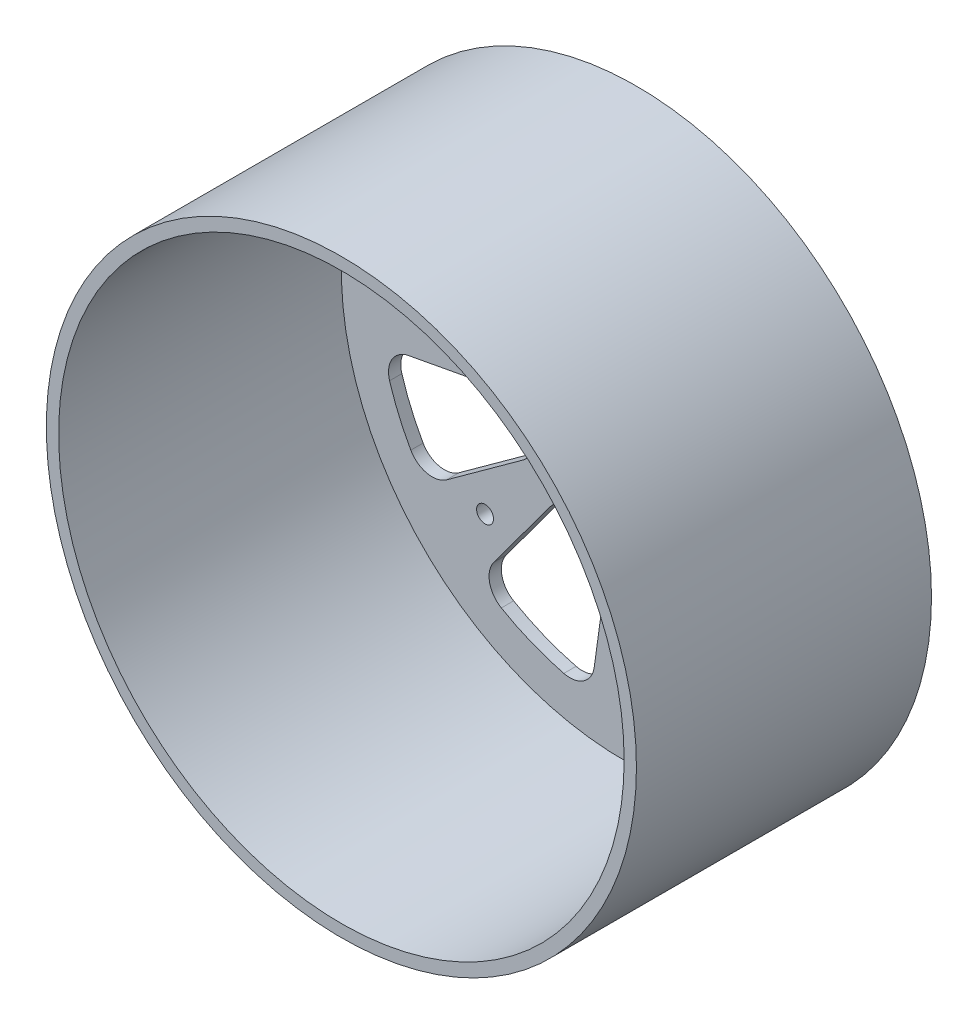
SolidWorks part; units mm, degrees
material "6061-T6 (SS)"
ref_plane "Front Plane" through (0, 0, 0) normal (0, 0, 1) x (1, 0, 0)
ref_plane "Top Plane" through (0, 0, 0) normal (0, 1, 0) x (1, 0, 0)
ref_plane "Right Plane" through (0, 0, 0) normal (1, 0, 0) x (0, 0, -1)
sketch "Sketch1" plane through (0, 0, 0) normal (0, 0, 1) x (1, 0, 0)
  circle A0 centre (0, 0) radius 76.2
  circle A1 centre (0, 0) radius 73.025
  dimension "D1" = 152.4
  dimension "D2" = 146.05
extrude "Boss-Extrude1" add sketch "Sketch1" along normal blind 76.2
sketch "Sketch3" plane through (0, 0, 0) normal (0, 0, 1) x (1, 0, 0)
  circle A0 centre (0, 0) radius 76.2
extrude "Boss-Extrude2" add sketch "Sketch3" along normal blind 3.175
sketch "Sketch4" plane through (0, 0, 3.175) normal (0, 0, 1) x (1, 0, 0)
  line L1 (-31.75, 31.75) -> (31.75, 31.75)
  line L2 (-31.75, 31.75) -> (-31.75, -31.75)
  line L3 (-31.75, -31.75) -> (31.75, -31.75)
  line L4 (31.75, 31.75) -> (31.75, -31.75)
  point P5 (0, 31.75)
  point P7 (-31.75, 0)
  dimension "D1" = 63.5
  dimension "2.5" = 63.5
extrude "Cut-Extrude1" [suppressed] cut sketch "Sketch4" against normal blind 1.27
sketch "Sketch5" plane through (0, 0, 3.175) normal (0, 0, 1) x (1, 0, 0)
  line L5 (-25.4, -25.4) -> (25.4, -25.4) construction
  line L6 (-25.4, -25.4) -> (-25.4, 25.4) construction
  line L7 (-25.4, 25.4) -> (25.4, 25.4) construction
  line L8 (25.4, -25.4) -> (25.4, 25.4) construction
  circle A0 centre (0, 37.813) radius 2.1828
  circle A1 centre (37.813, 0) radius 2.1828
  circle A2 centre (-37.813, 0) radius 2.1828
  circle A3 centre (0, -37.813) radius 2.1828
  point P20 (0, -25.4)
  point P21 (25.4, 0)
  dimension "D1" = 4.3656
  dimension "D2" = 4.3656
  dimension "D3" = 4.3656
  dimension "D4" = 4.3656
  dimension "D5" = 12.413
  dimension "D6" = 12.413
  dimension "D7" = 12.413
  dimension "D8" = 12.413
  dimension "D9" = 50.8
  dimension "D10" = 50.8
extrude "Cut-Extrude2" cut sketch "Sketch5" against normal through all contours L6 L5 L8 L7 | A1 | A0 | A2 | A3
sketch "Sketch10" plane through (0, 0, 76.2) normal (0, 0, 1) x (1, 0, 0)
  line L1 (71.6254, -14.2286) -> (73.6429, -1.5885)
  line L2 (73.6429, -1.5885) -> (72.1723, 11.1269)
  line L3 (72.1723, 11.1269) -> (69.745, 23.6947)
  line L4 (69.745, 23.6947) -> (64.0142, 35.1402)
  line L5 (64.0142, 35.1402) -> (57.4348, 46.1199)
  line L6 (57.4348, 46.1199) -> (48.135, 54.9151)
  line L7 (48.135, 54.9151) -> (38.1971, 62.9824)
  line L8 (38.1971, 62.9824) -> (26.45, 68.0665)
  line L9 (26.45, 68.0665) -> (14.3523, 72.2482)
  line L10 (14.3523, 72.2482) -> (1.5748, 73.008)
  line L11 (1.5748, 73.008) -> (-11.2236, 72.7999)
  line L12 (-11.2236, 72.7999) -> (-23.4904, 69.1437)
  line L16 (-23.4904, 69.1437) -> (-35.4458, 64.5708)
  line L17 (-35.4458, 64.5708) -> (-45.7223, 56.9396)
  line L18 (-45.7223, 56.9396) -> (-55.3927, 48.5536)
  line L19 (-55.3927, 48.5536) -> (-62.4394, 37.8678)
  line L20 (-62.4394, 37.8678) -> (-68.6584, 26.68)
  line L21 (-68.6584, 26.68) -> (-71.6254, 14.2286)
  line L22 (-71.6254, 14.2286) -> (-73.6429, 1.5885)
  line L23 (-73.6429, 1.5885) -> (-72.1723, -11.1269)
  line L24 (-72.1723, -11.1269) -> (-69.745, -23.6947)
  line L25 (-69.745, -23.6947) -> (-72.1723, -11.1269)
  line L26 (-72.1723, -11.1269) -> (-69.745, -23.6947)
  line L27 (-69.745, -23.6947) -> (-64.0142, -35.1402)
  line L28 (-64.0142, -35.1402) -> (-57.4348, -46.1199)
  line L29 (-57.4348, -46.1199) -> (-48.135, -54.9151)
  line L30 (-48.135, -54.9151) -> (-38.1971, -62.9824)
  line L31 (-38.1971, -62.9824) -> (-26.45, -68.0665)
  line L32 (-26.45, -68.0665) -> (-14.3523, -72.2482)
  line L33 (-14.3523, -72.2482) -> (-1.5748, -73.008)
  line L34 (-1.5748, -73.008) -> (11.2236, -72.7999)
  line L35 (11.2236, -72.7999) -> (23.4904, -69.1437)
  line L36 (23.4904, -69.1437) -> (35.4458, -64.5708)
  line L37 (35.4458, -64.5708) -> (45.7223, -56.9396)
  line L38 (45.7223, -56.9396) -> (55.3927, -48.5536)
  line L39 (55.3927, -48.5536) -> (62.4394, -37.8678)
  line L40 (62.4394, -37.8678) -> (68.6584, -26.68)
  line L41 (68.6584, -26.68) -> (71.6254, -14.2286)
  circle A7 centre (0, 0) radius 73.66 construction
  circle A8 centre (0, 0) radius 73.025 construction
  circle A9 centre (0, 0) radius 73.025 construction
  circle M41 centre (0, 0) radius 73.025
  dimension "D1" = 147.32
extrude "Cut-Extrude10" [suppressed] cut sketch "Sketch10" against normal up to surface (69.85 mm away) contours M41 | L20 L21 M41 | L18 L19 M41 | L16 L17 M41 | L11 L12 M41 | L9 L10 M41 | L7 L8 M41 | L5 L6 M41 | L3 L4 M41 | L1 L2 M41 | L40 L41 M41 | L38 L39 M41 | L36 L37 M41 | L34 L35 M41 | L32 L33 M41 | L30 L31 M41 | L28 L29 M41 | L24 L27 M41 | L22 L23 M41
fillet "Fillet1" [suppressed] radius 9.525
sketch "Sketch11" plane through (0, 0, 3.175) normal (0, 0, 1) x (1, 0, 0)
  line L0 (-71.842, 0) -> (0, 71.842) construction
  line L1 (0, 71.842) -> (71.842, 0) construction
  line L2 (71.842, 0) -> (0, -71.842) construction
  line L3 (0, -71.842) -> (-71.842, 0) construction
  line L4 (0, -37.813) -> (37.813, 0) construction
  circle A0 centre (-35.921, 35.921) radius 2.1828
  circle A1 centre (-35.921, -35.921) radius 2.1828
  circle A2 centre (35.921, -35.921) radius 2.1828
  circle A3 centre (35.921, 35.921) radius 2.1828
  dimension "D5" = 90
  dimension "D6" = 4.3656
  dimension "D7" = 4.3656
  dimension "D8" = 4.3656
  dimension "D9" = 4.3656
  dimension "D1" = 101.6
  dimension "D2" = 101.6
  dimension "D3" = 50.8
  dimension "D4" = 50.8
extrude "Cut-Extrude11" cut sketch "Sketch11" against normal through all
sketch "Sketch12" plane through (0, 0, 3.175) normal (0, 0, 1) x (1, 0, 0)
  circle A0 centre (0, 0) radius 18.9845
extrude "Cut-Extrude12" cut sketch "Sketch12" against normal through all
sketch "Sketch13" plane through (0, 0, 3.175) normal (0, 0, 1) x (1, 0, 0)
  line L0 (-18.8877, 26.0733) -> (-33.2138, 45.8495)
  line L1 (-5.8754, 31.655) -> (-10.3318, 55.665)
  line L2 (-45.5332, 33.6462) -> (-25.8934, 19.1336)
  line L3 (-31.8942, 4.3957) -> (-56.0856, 7.7297)
  arc A0 (-18.4226, 60.5815) -> (-31.2002, 55.1004) centre (0, 0) ccw
  arc A1 (-9.7737, 24.5951) -> (-11.0855, 24.0324) centre (0, 0) ccw
  arc A2 (-23.9264, 11.3124) -> (-25.0233, 8.6184) centre (0, 0) ccw
  arc A3 (-54.8027, 31.7202) -> (-61.3733, 15.583) centre (0, 0) ccw
  arc A4 (-5.8754, 31.655) -> (-9.7737, 24.5951) centre (-12.1187, 30.4962) cw
  arc A5 (-18.8877, 26.0733) -> (-11.0855, 24.0324) centre (-13.7452, 29.7985) ccw
  arc A6 (-25.8934, 19.1336) -> (-23.9264, 11.3124) centre (-29.6671, 14.0266) cw
  arc A7 (-31.8942, 4.3957) -> (-25.0233, 8.6184) centre (-31.0272, 10.6862) ccw
  arc A8 (-10.3318, 55.665) -> (-18.4226, 60.5815) centre (-16.5751, 54.5062) ccw
  arc A9 (-33.2138, 45.8495) -> (-31.2002, 55.1004) centre (-28.0714, 49.5748) cw
  arc A10 (-45.5332, 33.6462) -> (-54.8027, 31.7202) centre (-49.307, 28.5392) ccw
  arc A11 (-56.0856, 7.7297) -> (-61.3733, 15.583) centre (-55.2186, 14.0203) cw
  point P17 (-21.2852, 15.7284)
  point P26 (-50.9257, 37.6309)
  dimension "D1" = 6.35
extrude "Cut-Extrude13" cut sketch "Sketch13" against normal through all
pattern_circular "CirPattern1" count 4 over 360 about axis through (0, 0, 0) along (0, 0, 1) of "Cut-Extrude13"
sketch "Sketch14" plane through (0, 0, 0) normal (1, 0, 0) x (0, 0, -1)
  line L5 (-65.0875, 0) -> (-11.1125, 0) construction
  line L6 (-65.0875, 4.7625) -> (-11.1125, 4.7625)
  line L7 (-65.0875, -4.7625) -> (-11.1125, -4.7625)
  line L8 (-76.2, 76.2) -> (-76.2, -76.2) construction
  arc A0 (-65.0875, 4.7625) -> (-65.0875, -4.7625) centre (-65.0875, 0) ccw
  arc A1 (-11.1125, -4.7625) -> (-11.1125, 4.7625) centre (-11.1125, 0) ccw
  point P2 (-38.1, 0)
  dimension "D1" = 9.525
  dimension "D2" = 11.1125
  dimension "D3" = 11.1125
extrude "Cut-Extrude14" [suppressed] cut sketch "Sketch14" along normal up to next
pattern_circular "CirPattern2" [suppressed] count 14 over 360
equation "\"D2@Sketch14\"=3/16+.25"
equation "\"D3@Sketch14\"=3/16+.25"
